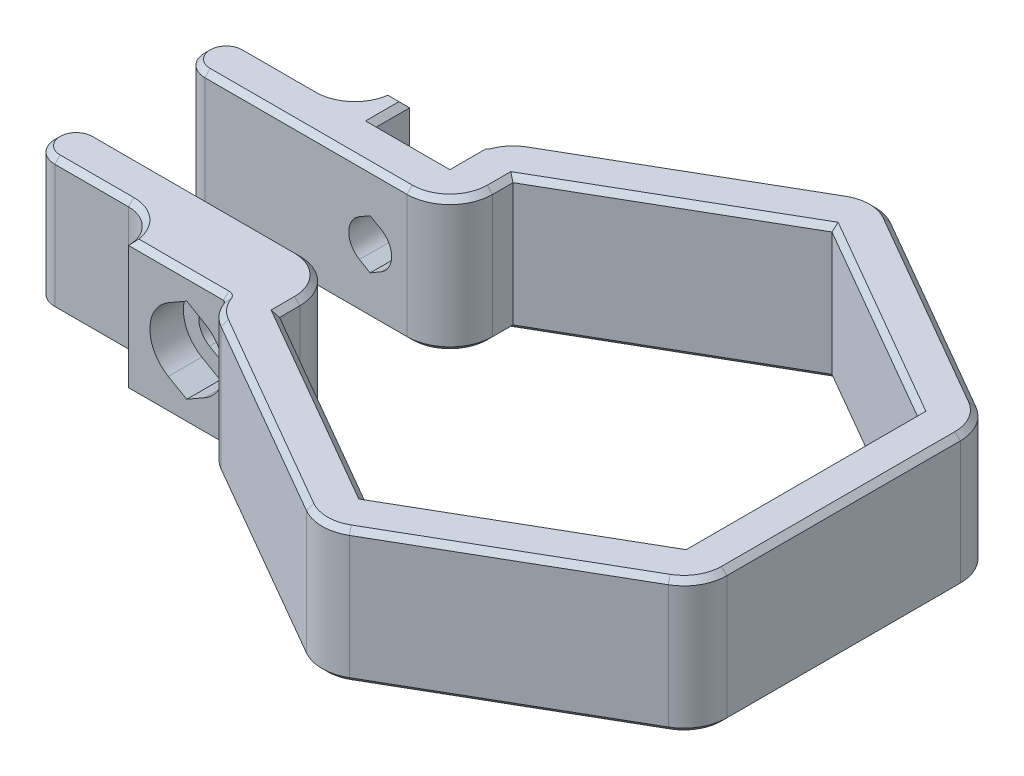
SolidWorks part; units mm, degrees
ref_plane "Front Plane" through (0, 0, 0) normal (0, 0, 1) x (1, 0, 0)
ref_plane "Top Plane" through (0, 0, 0) normal (0, 1, 0) x (1, 0, 0)
ref_plane "Right Plane" through (0, 0, 0) normal (1, 0, 0) x (0, 0, -1)
sketch "Sketch1" plane through (0, 0, 0) normal (0, 1, 0) x (1, 0, 0)
  line L0 (15.1, -8.718) -> (15.1, 8.718)
  line L1 (0, 17.3205) -> (-15, 8.6603) construction
  line L2 (-15, 8.6603) -> (-15, -8.6603) construction
  line L3 (-15, -8.6603) -> (0, -17.3205) construction
  line L4 (0, -17.3205) -> (15, -8.6603) construction
  line L5 (15, -8.6603) -> (15, 8.6603) construction
  line L6 (15, 8.6603) -> (0, 17.3205) construction
  line L7 (15.1, 8.718) -> (0, 17.436)
  line L8 (0, 17.436) -> (-15.1, 8.718)
  line L9 (-15.1, 8.718) -> (-15.1, 7.2)
  line L10 (-15.1, -8.718) -> (0, -17.436)
  line L11 (0, -17.436) -> (15.1, -8.718)
  line L12 (-1.6, 20.2073) -> (-16.7, 11.4893)
  line L14 (-16.7, -11.4893) -> (-1.6, -20.2073)
  line L15 (1.6, -20.2073) -> (16.7, -11.4893)
  line L16 (18.3, -8.718) -> (18.3, 8.718)
  line L17 (16.7, 11.4893) -> (1.6, 20.2073)
  line L18 (-18.3, 10.5655) -> (-18.3, -10.5655) construction
  line L19 (-18.3, -10.5655) -> (0, -21.131) construction
  line L20 (0, -21.131) -> (18.3, -10.5655) construction
  line L21 (18.3, -10.5655) -> (18.3, 10.5655) construction
  line L22 (18.3, 10.5655) -> (0, 21.131) construction
  line L23 (0, 21.131) -> (-18.3, 10.5655) construction
  line L24 (-33.4, 4) -> (-18.3, 4)
  line L25 (-33.4, 7.2) -> (-27.9, 7.2)
  line L26 (-15.1, 8.718) -> (-16.7, 11.4893) construction
  line L27 (-33.4, 7.2) -> (-33.4, 4) construction
  line L28 (-33.4, -7.2) -> (-27.9, -7.2)
  line L29 (-33.4, -4) -> (-18.3, -4)
  line L30 (-33.4, -4) -> (-33.4, -7.2) construction
  line L32 (-15.1, -7.2) -> (-15.1, -8.718)
  line L33 (-15.1, 8.718) -> (-15.1, -8.718) construction
  line L35 (-25.4, 9.7) -> (-18.3, 9.7)
  line L36 (-22.65, 4) -> (-22.65, 7.2) construction
  line L37 (-22.65, 7.2) -> (-23.8, 7.2) construction
  line L38 (-23.8, 7.2) -> (-23.8, 9.7) construction
  line L39 (-19.45, 4) -> (-19.45, 7.2) construction
  line L40 (-19.45, 7.2) -> (-18.3, 7.2) construction
  line L41 (-18.3, 7.2) -> (-18.3, 9.7) construction
  line L42 (-25.4, -9.7) -> (-18.3, -9.7)
  circle A0 centre (0, 0) radius 15 construction
  arc A1 (-18.0964, -9.8411) -> (-16.7, -11.4893) centre (-15.1, -8.718) ccw
  arc A7 (-33.4, 4) -> (-33.4, 7.2) centre (-33.4, 5.6) cw
  arc A8 (-33.4, -7.2) -> (-33.4, -4) centre (-33.4, -5.6) cw
  arc A9 (-18.3, 4) -> (-15.1, 7.2) centre (-18.3, 7.2) ccw
  arc A10 (-15.1, -7.2) -> (-18.3, -4) centre (-18.3, -7.2) ccw
  arc A11 (-27.9, 7.2) -> (-25.4, 9.7) centre (-27.9, 9.7) ccw
  arc A13 (-16.7, 11.4893) -> (-18.0964, 9.8411) centre (-15.1, 8.718) ccw
  arc A15 (-18.3, 9.7) -> (-18.0964, 9.8411) centre (-18.3, 9.9174) ccw
  arc A16 (-1.6, 20.2073) -> (1.6, 20.2073) centre (0, 17.436) cw
  arc A17 (16.7, 11.4893) -> (18.3, 8.718) centre (15.1, 8.718) cw
  arc A18 (18.3, -8.718) -> (16.7, -11.4893) centre (15.1, -8.718) cw
  arc A19 (1.6, -20.2073) -> (-1.6, -20.2073) centre (0, -17.436) cw
  arc A20 (-27.9, -7.2) -> (-25.4, -9.7) centre (-27.9, -9.7) cw
  arc A21 (-18.3, -9.7) -> (-18.0964, -9.8411) centre (-18.3, -9.9174) cw
  point P47 (-35, -5.6)
  point P57 (0, 0)
  point P64 (-18.3, 3.7035)
  point P65 (-18.5763, -9.7)
  point P66 (0, 0)
  point P67 (0, 0)
  dimension "D4" = 8
  dimension "D1" = 30
  dimension "D5" = 20
  dimension "D6" = 5.5
  dimension "D7" = 1.6
  dimension "D8" = 3.2
  dimension "D9" = 2.5
  dimension "D2" = 0.1
  dimension "D3" = 3.2
extrude "Boss-Extrude1" add sketch "Sketch1" along normal blind 10
sketch "Sketch3" plane through (0, 0, -9.7) normal (0, 0, -1) x (-1, 0, 0)
  line L0 (18.3, 10) -> (25.4, 10) construction
  line L1 (18.3, 0) -> (23.8, 0)
  line L2 (18.3, 0) -> (18.3, 10)
  line L3 (18.3, 10) -> (23.8, 10)
  line L4 (23.8, 0) -> (23.8, 10)
  point P7 (23.8, 0)
extrude "Cut-Extrude1" cut sketch "Sketch3" against normal up to vertex (2.5 mm away) up to point (-19.45, 0, -7.2)
sketch "Sketch4" plane through (0, 0, -7.2) normal (0, 0, -1) x (-1, 0, 0)
  line L0 (18.3, 10) -> (23.8, 0) construction
  line L1 (20.25, 6.3856) -> (21.05, 6.8475)
  line L2 (21.05, 6.8475) -> (21.85, 6.3856)
  line L3 (20.25, 3.6144) -> (21.05, 3.1525)
  line L4 (21.05, 3.1525) -> (21.85, 3.6144)
  arc A0 (20.25, 6.3856) -> (20.25, 3.6144) centre (21.05, 5) ccw
  arc A1 (21.85, 3.6144) -> (21.85, 6.3856) centre (21.05, 5) ccw
  point P5 (19.45, 5)
  point P11 (0, 0)
  dimension "D1" = 120
extrude "Cut-Extrude2" cut sketch "Sketch4" against normal through all
sketch "Sketch5" plane through (0, 0, 9.7) normal (0, 0, 1) x (1, 0, 0)
  line L0 (-18.3, 10) -> (-18.3, 0) construction
  line L1 (-21.05, 6.8475) -> (-20.25, 6.3856) construction
  line L2 (-21.85, 6.3856) -> (-21.05, 6.8475) construction
  line L3 (-20.25, 3.6144) -> (-21.05, 3.1525) construction
  line L4 (-21.05, 3.1525) -> (-21.85, 3.6144) construction
  line L24 (-22.425, 2.6184) -> (-21.05, 1.8246)
  line L25 (-21.05, 1.8246) -> (-19.675, 2.6184)
  line L26 (-19.675, 7.3816) -> (-21.05, 8.1754)
  line L27 (-21.05, 8.1754) -> (-22.425, 7.3816)
  arc A0 (-20.25, 3.6144) -> (-20.25, 6.3856) centre (-21.05, 5) ccw construction
  arc A1 (-21.85, 6.3856) -> (-21.85, 3.6144) centre (-21.05, 5) ccw construction
  arc A9 (-22.425, 7.3816) -> (-22.425, 2.6184) centre (-21.05, 5) ccw
  arc A10 (-19.675, 2.6184) -> (-19.675, 7.3816) centre (-21.05, 5) ccw
  point P16 (-20.7934, 8.9773)
  point P17 (-22.7219, 8.8458)
extrude "Cut-Extrude3" cut sketch "Sketch5" against normal up to vertex (2.5 mm away) up to point (-27.9, 10, 7.2)
chamfer "Chamfer1" distance 0.4 angle 45 70 edges at (-23.8, 0, -8.45) (-24.6, 0, -9.7) (-26.1322, 0, -7.9322) (-30.65, 0, -7.2) (-35, 0, -5.6) (-25.85, 0, -4) (-16.0373, 0, -4.9373) (-15.1, 0, -7.959) (-7.55, 0, -13.077) (7.55, 0, -13.077) (15.1, 0, 0) (7.55, 0, 13.077) (-7.55, 0, 13.077) (-15.1, 0, 7.959) (-16.0373, 0, 4.9373) (-25.85, 0, 4) (-35, 0, 5.6) (-30.65, 0, 7.2) (-26.1322, 0, 7.9322) (-21.85, 0, 9.7) (-18.1762, 0, 9.7387) (-17.5415, 0, 10.7866) (-9.15, 0, 15.8483) (0, 0, 20.636) (9.15, 0, 15.8483) (17.8713, 0, 10.318) (18.3, 0, 0) (17.8713, 0, -10.318) (9.15, 0, -15.8483) (0, 0, -20.636) (-9.15, 0, -15.8483) (-17.5415, 0, -10.7866) (-18.1762, 0, -9.7387) (-18.3, 0, -8.45) (-21.05, 0, -7.2) (-18.1762, 10, -9.7387) (-17.5415, 10, -10.7866) (-9.15, 10, -15.8483) (0, 10, -20.636) (9.15, 10, -15.8483) (17.8713, 10, -10.318) (18.3, 10, 0) (17.8713, 10, 10.318) (9.15, 10, 15.8483) (0, 10, 20.636) (-9.15, 10, 15.8483) (-17.5415, 10, 10.7866) (-18.1762, 10, 9.7387) (-21.85, 10, 9.7) (-26.1322, 10, 7.9322) (-30.65, 10, 7.2) (-35, 10, 5.6) (-25.85, 10, 4) (-16.0373, 10, 4.9373) (-15.1, 10, 7.959) (-7.55, 10, 13.077) (7.55, 10, 13.077) (15.1, 10, 0) (7.55, 10, -13.077) (-7.55, 10, -13.077) (-15.1, 10, -7.959) (-16.0373, 10, -4.9373) (-25.85, 10, -4) (-35, 10, -5.6) (-30.65, 10, -7.2) (-26.1322, 10, -7.9322) (-24.6, 10, -9.7) (-23.8, 10, -8.45) (-21.05, 10, -7.2) (-18.3, 10, -8.45)
